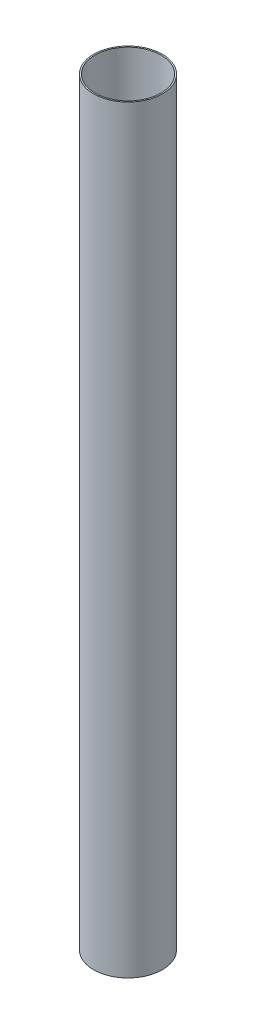
SolidWorks part; units mm, degrees
material "Thornel Mat VMA"
ref_plane "Front Plane" through (0, 0, 0) normal (0, 0, 1) x (1, 0, 0)
ref_plane "Top Plane" through (0, 0, 0) normal (0, 1, 0) x (1, 0, 0)
ref_plane "Right Plane" through (0, 0, 0) normal (1, 0, 0) x (0, 0, -1)
other "Center of Mass"
sketch "Sketch1" plane through (0, 0, 0) normal (0, 1, 0) x (1, 0, 0)
  circle A0 centre (0, 0) radius 76.2
  circle A1 centre (0, 0) radius 79.375
extrude "Boss-Extrude1" add sketch "Sketch1" along normal blind 1752.6
